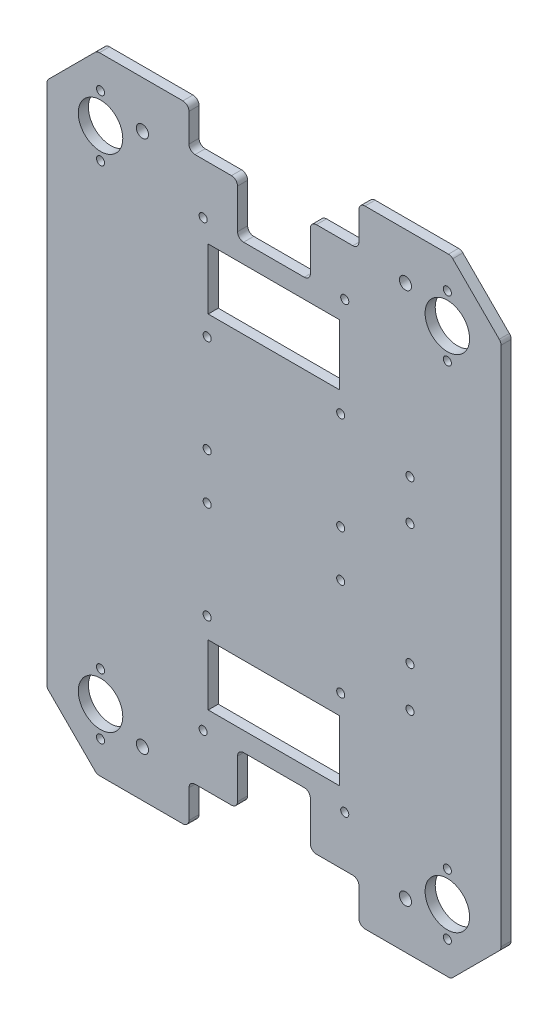
SolidWorks part; units mm, degrees
material "Alliage 1060"
ref_plane "Plan de dessus" through (0, 0, 0) normal (0, 0, 1) x (1, 0, 0)
ref_plane "Plan de droite" through (0, 0, 0) normal (0, 1, 0) x (1, 0, 0)
ref_plane "Plan de face" through (0, 0, 0) normal (1, 0, 0) x (0, 0, -1)
sketch "Esquisse1" plane through (0, 0, 0) normal (0, 0, 1) x (1, 0, 0)
  line L0 (0, 0) -> (-175, 0)
  line L1 (-175, 0) -> (-199.7487, 24.7487)
  line L2 (-199.7487, 24.7487) -> (-199.7487, 284.7487)
  line L3 (-199.7487, 284.7487) -> (-175, 309.4975)
  line L4 (-175, 309.4975) -> (0, 309.4975)
  line L5 (0, 309.4975) -> (24.7487, 284.7487)
  line L6 (24.7487, 284.7487) -> (24.7487, 24.7487)
  line L7 (24.7487, 24.7487) -> (0, 0)
  dimension "D1" = 260
  dimension "D2" = 35
  dimension "D3" = 135
  dimension "D4" = 175
extrude "Base" add sketch "Esquisse1" along normal blind 5
sketch "Esquisse3" plane through (0, 0, 0) normal (0, 0, -1) x (-1, 0, 0)
  line L0 (129.5, 0) -> (129.5, 20)
  line L1 (175, 0) -> (0, 0) construction
  line L2 (129.5, 20) -> (105.5, 20)
  line L3 (105.5, 20) -> (105.5, 45.5)
  line L4 (105.5, 45.5) -> (69.5, 45.5)
  line L5 (69.5, 45.5) -> (69.5, 20)
  line L6 (69.5, 20) -> (45.5, 20)
  line L7 (45.5, 20) -> (45.5, 0)
  line L8 (-24.7487, 154.7487) -> (199.7487, 154.7487) construction
  line L9 (-24.7487, 24.7487) -> (-24.7487, 284.7487) construction
  line L10 (199.7487, 284.7487) -> (199.7487, 24.7487) construction
  line L11 (45.5, 0) -> (129.5, 0)
  line L12 (45.5, 309.4975) -> (129.5, 309.4975)
  line L13 (129.5, 309.4975) -> (129.5, 289.4975)
  line L14 (129.5, 289.4975) -> (105.5, 289.4975)
  line L15 (105.5, 289.4975) -> (105.5, 263.9975)
  line L16 (105.5, 263.9975) -> (69.5, 263.9975)
  line L17 (69.5, 263.9975) -> (69.5, 289.4975)
  line L18 (69.5, 289.4975) -> (45.5, 289.4975)
  line L19 (45.5, 289.4975) -> (45.5, 309.4975)
  line L20 (87.5, 45.5) -> (87.5, -49954.5) construction
  line L21 (0, 309.4975) -> (175, 309.4975) construction
  line L22 (55, 254.4975) -> (120, 254.4975)
  line L23 (55, 254.4975) -> (55, 224.4975)
  line L24 (55, 224.4975) -> (120, 224.4975)
  line L25 (120, 254.4975) -> (120, 224.4975)
  line L26 (120, 55) -> (120, 85)
  line L27 (55, 85) -> (120, 85)
  line L28 (55, 55) -> (120, 55)
  line L29 (55, 55) -> (55, 85)
  circle A0 centre (52.5, 45) radius 2
  circle A1 centre (122.5, 45) radius 2
  circle A2 centre (122.5, 264.4975) radius 2
  circle A3 centre (52.5, 264.4975) radius 2
  point P4 (87.5, 45.5)
  point P11 (87.5, 0)
  point P40 (87.5, 254.4975)
  dimension "D7" = 4
  dimension "D5" = 25
  dimension "D1" = 20
  dimension "D2" = 24
  dimension "D3" = 36
  dimension "D4" = 25.5
  dimension "D6" = 7
  dimension "D8" = 55
  dimension "D9" = 30
  dimension "D10" = 65
extrude "Enlèv. mat.-Extru.1" cut sketch "Esquisse3" against normal through all
fillet "Congé1" radius 3 24 edges at (-199.7487, 24.7487, 2.5) (24.7487, 24.7487, 2.5) (0, 0, 2.5) (-129.5, 20, 2.5) (-105.5, 45.5, 2.5) (-105.5, 20, 2.5) (-175, 0, 2.5) (-129.5, 0, 2.5) (-69.5, 45.5, 2.5) (-45.5, 20, 2.5) (-69.5, 20, 2.5) (-45.5, 0, 2.5) (24.7487, 284.7487, 2.5) (-129.5, 289.4975, 2.5) (-105.5, 263.9975, 2.5) (-199.7487, 284.7487, 2.5) (-175, 309.4975, 2.5) (-129.5, 309.4975, 2.5) (-105.5, 289.4975, 2.5) (-69.5, 263.9975, 2.5) (-45.5, 289.4975, 2.5) (-69.5, 289.4975, 2.5) (-45.5, 309.4975, 2.5) (0, 309.4975, 2.5)
sketch "Esquisse6" plane through (0, 0, 5) normal (0, 0, 1) x (1, 0, 0)
  line L0 (-173.2157, 263.4975) -> (-173.2157, 278.4975) construction
  line L2 (-87.5, 231.5685) -> (-87.5, -49768.4315) construction
  line L4 (-55, 224.4975) -> (-120, 224.4975) construction
  line L5 (-203.2843, 154.7487) -> (49796.7157, 154.7487) construction
  line L6 (-199.7487, 283.5061) -> (-199.7487, 25.9914) construction
  line L7 (-1.7843, 293.4975) -> (-1.7843, 263.4975) construction
  line L8 (-1.7843, 46) -> (-1.7843, 16) construction
  line L9 (-42.5, 0) -> (-1.2426, 0) construction
  line L11 (-173.2157, 46) -> (-173.2157, 31) construction
  line L13 (-173.2157, 31) -> (-173.2157, 16) construction
  line L15 (-173.7574, 0) -> (-132.5, 0) construction
  line L18 (-132.5, 309.4975) -> (-173.7574, 309.4975) construction
  circle A2 centre (-1.7843, 16) radius 2
  circle A3 centre (-1.7843, 46) radius 2
  circle A4 centre (-1.7843, 263.4975) radius 2
  circle A5 centre (-1.7843, 293.4975) radius 2
  circle A10 centre (-1.7843, 278.4975) radius 11
  circle A11 centre (-1.7843, 31) radius 11
  circle A25 centre (-173.2157, 16) radius 2
  circle A26 centre (-173.2157, 46) radius 2
  circle A27 centre (-173.2157, 31) radius 11
  circle A28 centre (-173.2157, 263.4975) radius 2
  circle A29 centre (-173.2157, 293.4975) radius 2
  circle A30 centre (-173.2157, 278.4975) radius 11
  point P15 (-87.5, 224.4975)
  point P20 (-199.7487, 154.7487)
  dimension "D2" = 15
  dimension "D3" = 22
  dimension "D4" = 30
  dimension "D5" = 31
  dimension "D7" = 31
  dimension "D8" = 22
  dimension "D10" = 30
  dimension "D6" = 22
  dimension "D13" = 22
  dimension "D14" = 30
  dimension "D15" = 31
extrude "Perçage pour billes" cut sketch "Esquisse6" against normal up to next
sketch "Esquisse8" plane through (0, 0, 5) normal (0, 0, 1) x (1, 0, 0)
  line L0 (-87.5, 263.9975) -> (-87.5, 85) construction
  line L1 (-72.5, 263.9975) -> (-102.5, 263.9975) construction
  line L2 (-120, 85) -> (-55, 85) construction
  line L3 (-132.5, 309.4975) -> (-173.7574, 309.4975) construction
  line L4 (-129.5, 292.4975) -> (-129.5, 306.4975) construction
  line L5 (-173.7574, 0) -> (-132.5, 0) construction
  line L6 (-129.5, 3) -> (-129.5, 17) construction
  line L8 (-199.7487, 283.5061) -> (-199.7487, 25.9914) construction
  circle A0 centre (-152.5, 23) radius 3
  circle A1 centre (-152.5, 286.4975) radius 3
  circle A2 centre (-22.5, 286.4975) radius 3
  circle A3 centre (-22.5, 23) radius 3
  dimension "D1" = 23
  dimension "D2" = 23
  dimension "D3" = 6
  dimension "D4" = 23
  dimension "D5" = 23
  dimension "D6" = 6
extrude "Perçage pour profilé" cut sketch "Esquisse8" against normal up to next
sketch "Esquisse10" plane through (0, 0, 5) normal (0, 0, 1) x (1, 0, 0)
  line L0 (-199.7487, 283.5061) -> (-199.7487, 25.9914) construction
  line L2 (-55, 224.4975) -> (-120, 224.4975) construction
  line L3 (-87.5, 224.4975) -> (-87.5, 85) construction
  line L4 (-120, 85) -> (-55, 85) construction
  line L5 (-199.7487, 154.7487) -> (24.7487, 154.7487) construction
  line L6 (24.7487, 25.9914) -> (24.7487, 283.5061) construction
  circle A0 centre (-120.5, 214.4975) radius 2
  circle A1 centre (-120.5, 166.1975) radius 2
  circle A2 centre (-54.5, 166.1975) radius 2
  circle A3 centre (-54.5, 214.4975) radius 2
  circle A4 centre (-54.5, 143.3) radius 2
  circle A5 centre (-54.5, 95) radius 2
  circle A6 centre (-120.5, 143.3) radius 2
  circle A7 centre (-120.5, 95) radius 2
  dimension "D1" = 48.3
  dimension "D2" = 33
  dimension "D3" = 4
  dimension "D4" = 4
  dimension "D5" = 10
extrude "Enlèv. mat.-Extru.3" cut sketch "Esquisse10" against normal through all
sketch "Esquisse13" plane through (0, 0, 5) normal (0, 0, 1) x (1, 0, 0)
  line L0 (24.7487, 154.7487) -> (-199.7487, 154.7487) construction
  line L1 (24.7487, 25.9914) -> (24.7487, 283.5061) construction
  line L2 (-199.7487, 283.5061) -> (-199.7487, 25.9914) construction
  circle A0 centre (-20.2513, 204.7487) radius 2
  circle A1 centre (-20.2513, 184.7487) radius 2
  circle A2 centre (-20.2513, 124.7487) radius 2
  circle A3 centre (-20.2513, 104.7487) radius 2
  dimension "D1" = 4
  dimension "D2" = 4
  dimension "D3" = 20
  dimension "D4" = 30
  dimension "D5" = 45
extrude "Enlèv. mat.-Extru.4" cut sketch "Esquisse13" against normal blind 10
